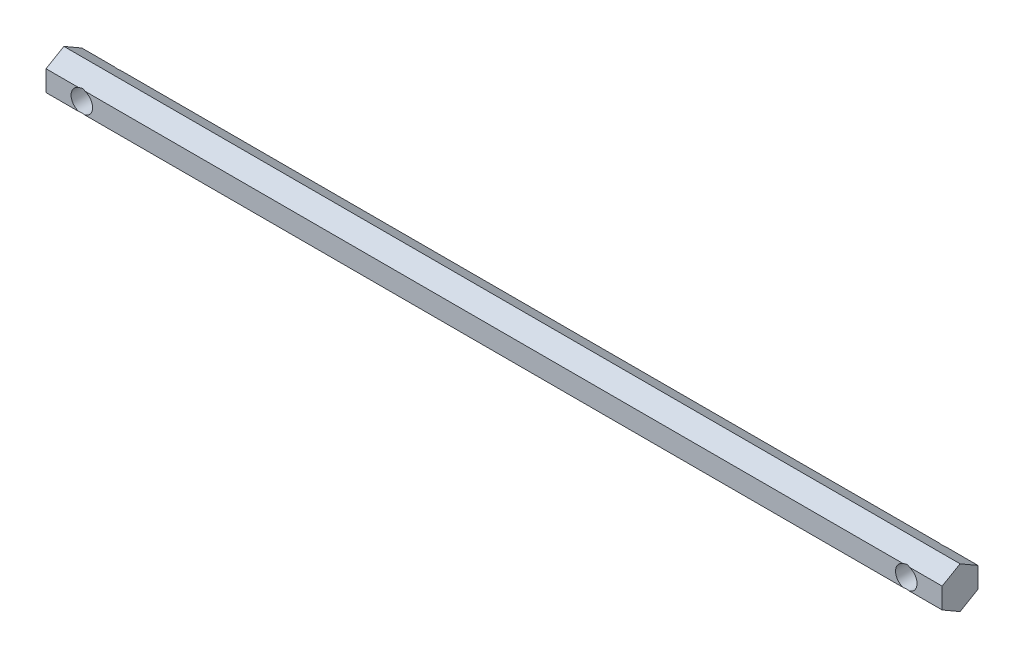
SolidWorks part; units mm, degrees
ref_plane "Plano frontal" through (0, 0, 0) normal (0, 0, 1) x (1, 0, 0)
ref_plane "Plano superior" through (0, 0, 0) normal (0, 1, 0) x (1, 0, 0)
ref_plane "Plano direito" through (0, 0, 0) normal (1, 0, 0) x (0, 0, -1)
sketch "Sketch1" plane through (0, 0, 0) normal (1, 0, 0) x (0, 0, -1)
  line L1 (0, 5.7735) -> (-5, 2.8868)
  line L2 (-5, 2.8868) -> (-5, -2.8868)
  line L3 (-5, -2.8868) -> (0, -5.7735)
  line L4 (0, -5.7735) -> (5, -2.8868)
  line L5 (5, -2.8868) -> (5, 2.8868)
  line L6 (5, 2.8868) -> (0, 5.7735)
  circle A0 centre (0, 0) radius 5 construction
  dimension "D1" = 10
extrude "Boss-Extrude1" add sketch "Sketch1" along normal mid plane 250
sketch "Sketch2" plane through (0, 0, 0) normal (0, 0, 1) x (1, 0, 0)
  line L0 (0, 52.8546) -> (0, -40.3924) construction
  line L1 (-150.297, 0) -> (146.8781, 0) construction
  circle A0 centre (-115, 0) radius 3
  circle A1 centre (115, 0) radius 3
  dimension "D1" = 6
  dimension "D2" = 6
  dimension "D3" = 115
  dimension "D4" = 115
extrude "Cut-Extrude1" cut sketch "Sketch2" against normal through all both and the other way through all
